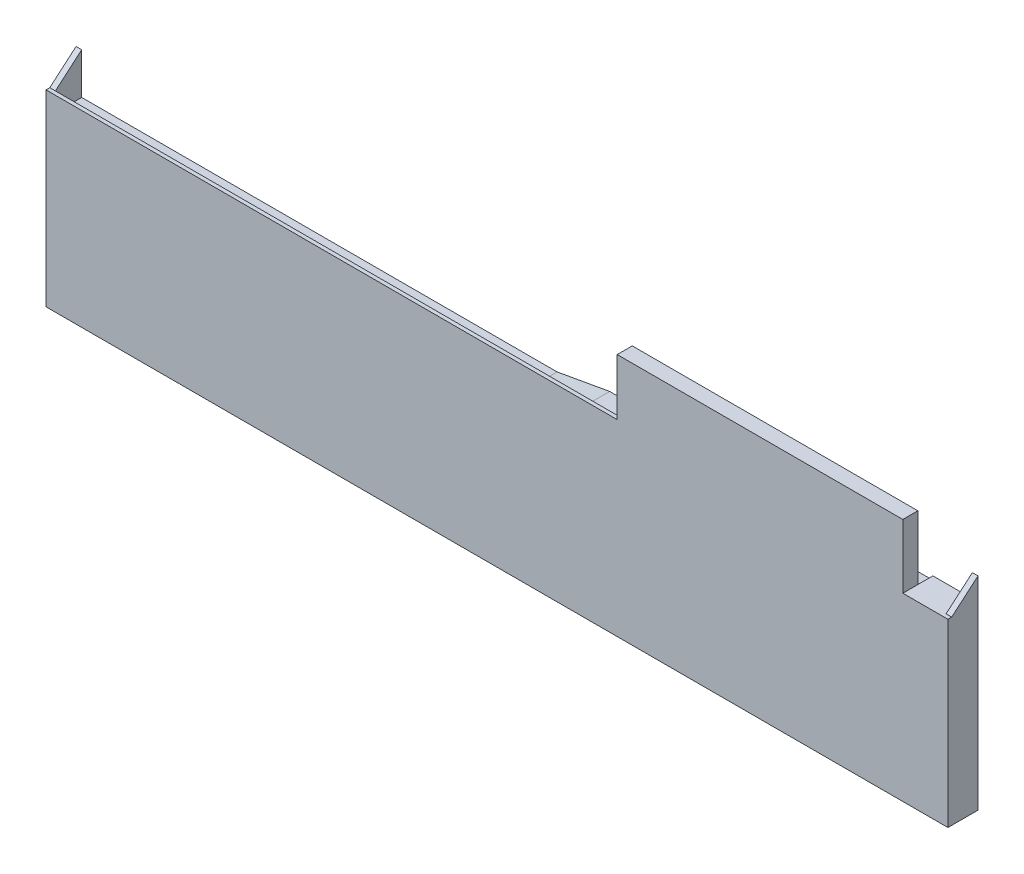
SolidWorks part; units mm, degrees
ref_plane "Alzado" through (0, 0, 0) normal (0, 0, 1) x (1, 0, 0)
ref_plane "Planta" through (0, 0, 0) normal (0, 1, 0) x (1, 0, 0)
ref_plane "Vista lateral" through (0, 0, 0) normal (1, 0, 0) x (0, 0, -1)
sketch "Croquis2" plane through (0, 0, 0) normal (0, 0, 1) x (1, 0, 0)
  line L0 (0, 0) -> (240, 0)
  line L1 (0, 0) -> (0, 50)
  line L2 (0, 50) -> (152, 50)
  line L3 (152, 50) -> (152, 65)
  line L4 (152, 65) -> (228, 65)
  line L5 (228, 65) -> (228, 48)
  line L6 (152, 50) -> (228, 50) construction
  line L7 (240, 0) -> (240, 48)
  line L8 (228, 48) -> (240, 48)
  dimension "D1" = 240
  dimension "D2" = 50
  dimension "D3" = 152
  dimension "D4" = 15
  dimension "D5" = 76
  dimension "D6" = 17
  dimension "D7" = 48
extrude "Saliente-Extruir1" add sketch "Croquis2" along normal blind 8
sketch "Croquis6" plane through (0, 50, 0) normal (0, 1, 0) x (1, 0, 0)
  line L0 (0, -8) -> (0, -7) construction
  line L1 (0, -8) -> (0, 0) construction
  line L2 (152, -8) -> (152, -7) construction
  line L3 (152, -8) -> (152, 0) construction
  line L4 (152, -7) -> (0, -7)
  line L5 (0, -7) -> (0, -5.5)
  line L6 (152, -7) -> (152, -5.5)
  line L7 (152, -5.5) -> (0, -5.5)
  dimension "D1" = 1
  dimension "D2" = 1
  dimension "D3" = 1.5
  dimension "D4" = 1.5
extrude "Cortar-Extruir10" cut sketch "Croquis6" against normal blind 1.5
sketch "Croquis8" plane through (0, 0, 0) normal (-1, 0, 0) x (0, 0, 1)
  line L0 (1.4889, 48.7041) -> (1.3306, 48.8624) construction
sketch "Croquis9" plane through (0, 0, 0) normal (-1, 0, 0) x (0, 0, 1)
  line L0 (5.5, 48.5) -> (5.5, 46.5) construction
  line L1 (5.5, 48.5) -> (5.5, 46.5)
  line L2 (5.5, 46.5) -> (6.5, 46.5)
  line L3 (6.5, 46.5) -> (6.5, 45)
  line L4 (6.5, 45) -> (0, 45)
  line L5 (0, 50) -> (0, 0) construction
  line L6 (0, 45) -> (0, 50)
  line L7 (0, 50) -> (5.5, 50)
  line L8 (5.5, 50) -> (5.5, 48.5)
  dimension "D1" = 2
  dimension "D2" = 1
  dimension "D3" = 1.5
extrude "Cortar-Extruir12" cut sketch "Croquis9" against normal blind 128
sketch "Croquis12" plane through (0, 50, 0) normal (0, 1, 0) x (1, 0, 0)
  line L0 (152, -5.5) -> (152, 0)
  line L1 (152, 0) -> (128, 0)
  line L2 (128, 0) -> (128, -5.5)
  line L3 (128, -5.5) -> (152, -5.5)
extrude "Cortar-Extruir13" cut sketch "Croquis12" against normal blind 1.5
sketch "Croquis13" plane through (0, 0, 0) normal (0, 0, -1) x (-1, 0, 0)
  line L1 (-152, 48.5) -> (-128, 48.5) construction
  line L3 (-142, 48.5) -> (-128, 45)
  line L4 (-128, 45) -> (-128, 48.5)
  line L5 (-128, 48.5) -> (-142, 48.5)
extrude "Cortar-Extruir14" cut sketch "Croquis13" against normal blind 5.5
sketch "Croquis14" plane through (0, 0, 5.5) normal (0, 0, -1) x (-1, 0, 0)
  line L0 (-128, 45) -> (-128, 46.5)
  line L1 (-128, 46.5) -> (-134, 46.5)
  line L2 (-142, 48.5) -> (-128, 45) construction
  line L3 (-134, 46.5) -> (-128, 45)
extrude "Cortar-Extruir16" cut sketch "Croquis14" against normal blind 1.5
sketch "Croquis17" plane through (0, 65, 0) normal (0, 1, 0) x (1, 0, 0)
  line L1 (228, 0) -> (152, 0)
  line L3 (228, -4) -> (152, -4)
  line L4 (152, 0) -> (152, -4)
  line L8 (228, -4) -> (228, 0)
  line L9 (228, -8) -> (228, 0) construction
extrude "Cortar-Extruir17" cut sketch "Croquis17" against normal blind 18
sketch "Croquis18" plane through (0, 48.5, 0) normal (0, 1, 0) x (1, 0, 0)
  line L0 (142, -5.5) -> (152, -5.5) construction
  line L1 (152, -7) -> (152, -4) construction
  line L2 (152, -5.5) -> (152, 0)
  line L3 (152, 0) -> (142, 0)
  line L4 (142, 0) -> (142, -5.5)
  line L5 (142, -5.5) -> (152, -5.5)
extrude "Cortar-Extruir18" cut sketch "Croquis18" against normal blind 1
sketch "Croquis19" plane through (0, 0, 0) normal (0, 0, -1) x (-1, 0, 0)
  line L0 (-142, 47.5) -> (-128, 45)
  line L1 (-128, 45) -> (-142, 48.5)
  line L2 (-142, 48.5) -> (-142, 47.5)
extrude "Cortar-Extruir22" cut sketch "Croquis19" against normal blind 5
sketch "Croquis20" plane through (0, 0, 5) normal (0, 0, -1) x (-1, 0, 0)
  line L0 (-142, 48.5) -> (-142, 47.5)
  line L1 (-142, 47.5) -> (-128, 45) construction
  line L2 (-142, 48.5) -> (-142, 47.5) construction
  line L3 (-142, 47.5) -> (-128, 45)
  line L4 (-128, 45) -> (-142, 48.5)
extrude "Cortar-Extruir23" cut sketch "Croquis20" against normal blind 0.5
sketch "Croquis21" plane through (0, 0, 5.5) normal (0, 0, -1) x (-1, 0, 0)
  line L0 (-134, 46.5) -> (-136.4, 46.5)
  line L1 (-142, 47.5) -> (-128, 45) construction
  line L2 (-136.4, 46.5) -> (-134, 46.0714)
  line L3 (-134, 46.0714) -> (-128, 45)
  line L4 (-128, 45) -> (-134, 46.5)
extrude "Cortar-Extruir25" cut sketch "Croquis21" against normal blind 1.5
sketch "Croquis22" plane through (240, 0, 0) normal (1, 0, 0) x (0, 0, -1)
  line L0 (0, 48) -> (0, 54)
  line L3 (0, 54) -> (-7, 48)
  line L4 (-8, 48) -> (-4, 48) construction
  line L5 (0, 48) -> (-7, 48)
  dimension "D1" = 6
  dimension "D2" = 1
extrude "Saliente-Extruir3" add sketch "Croquis22" against normal blind 1.5
sketch "Croquis23" plane through (0, 0, 0) normal (-1, 0, 0) x (0, 0, 1)
  line L1 (0, 48) -> (0, 54) construction
  line L2 (0, 50) -> (0, 56)
  line L3 (0, 56) -> (7, 50)
  line L4 (0, 50) -> (0, 45)
  line L5 (0, 45) -> (6.5, 45)
  line L6 (6.5, 45) -> (6.5, 46.5)
  line L7 (6.5, 46.5) -> (5.5, 46.5)
  line L8 (5.5, 47.5) -> (5.5, 46.5) construction
  line L9 (5.5, 46.5) -> (5.5, 48.5) construction
  line L10 (5.5, 46.5) -> (5.5, 48.5)
  line L11 (5.5, 48.5) -> (7, 48.5)
  line L12 (7, 48.5) -> (7, 50)
  dimension "D1" = 6
  dimension "D2" = 6
extrude "Saliente-Extruir4" add sketch "Croquis23" against normal blind 1.5
